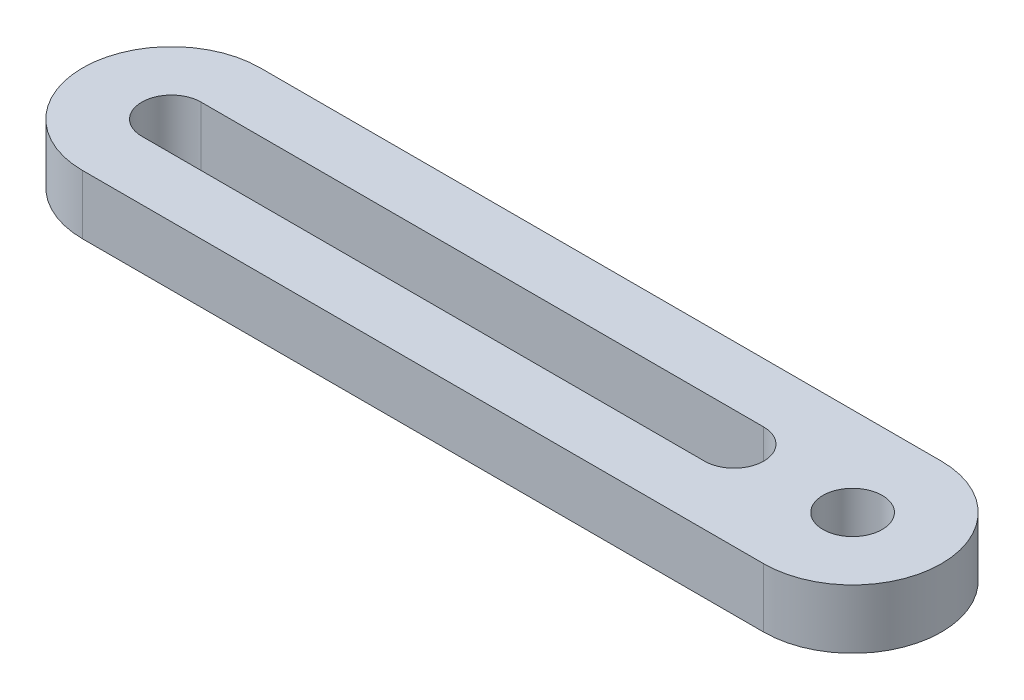
SolidWorks part; units mm, degrees
ref_plane "Front Plane" through (0, 0, 0) normal (0, 0, 1) x (1, 0, 0)
ref_plane "Top Plane" through (0, 0, 0) normal (0, 1, 0) x (1, 0, 0)
ref_plane "Right Plane" through (0, 0, 0) normal (1, 0, 0) x (0, 0, -1)
sketch "Sketch1" plane through (0, 0, 0) normal (0, 1, 0) x (1, 0, 0)
  line L0 (0, 0) -> (115, 0) construction
  line L1 (0, 15) -> (115, 15)
  line L2 (0, -15) -> (115, -15)
  line L3 (0, 0) -> (95, 0) construction
  line L4 (0, 5) -> (95, 5)
  line L5 (0, -5) -> (95, -5)
  arc A0 (0, 15) -> (0, -15) centre (0, 0) ccw
  arc A1 (115, -15) -> (115, 15) centre (115, 0) ccw
  arc A2 (0, 5) -> (0, -5) centre (0, 0) ccw
  circle A3 centre (115, 0) radius 5
  arc A4 (95, -5) -> (95, 5) centre (95, 0) ccw
  point P3 (57.5, 0)
  point P12 (47.5, 0)
  dimension "D1" = 5
  dimension "D2" = 10
  dimension "D3" = 20
  dimension "D5" = 15
  dimension "D4" = 95
extrude "Boss-Extrude1" add sketch "Sketch1" along normal blind 10
